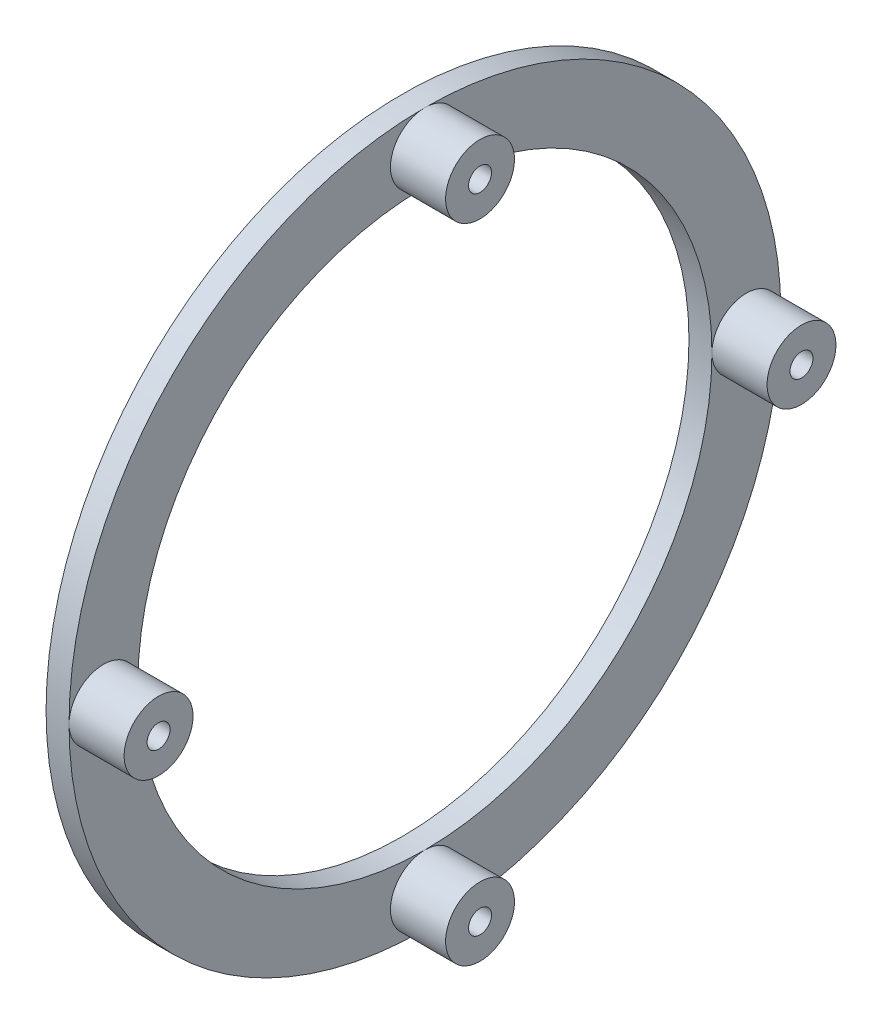
SolidWorks part; units mm, degrees
material "6061-T6 (SS)"
ref_plane "Front Plane" through (0, 0, 0) normal (0, 0, 1) x (1, 0, 0)
ref_plane "Top Plane" through (0, 0, 0) normal (0, 1, 0) x (1, 0, 0)
ref_plane "Right Plane" through (0, 0, 0) normal (1, 0, 0) x (0, 0, -1)
sketch "Sketch1" plane through (0, 0, 0) normal (1, 0, 0) x (0, 0, -1)
  circle A0 centre (0, 0) radius 98.425
  circle A1 centre (0, 0) radius 79.375
  dimension "D1" = 196.85
  dimension "D2" = 158.75
extrude "Boss-Extrude1" add sketch "Sketch1" along normal blind 6.35
sketch "Sketch2" plane through (0, 0, 0) normal (1, 0, 0) x (0, 0, -1)
  circle A0 centre (0, 0) radius 88.9 construction
  circle A1 centre (88.9, 0) radius 9.525
  dimension "D1" = 177.8
  dimension "D2" = 19.05
extrude "Boss-Extrude2" add sketch "Sketch2" along normal blind 15.24 from surface at 6.35 starting at face at (6.35, 0, -98.425)
hole_wizard "1/4 (0.2500) Dowel Hole1" positions "Sketch3" profile "Sketch4" hole size "1/4" standard "ANSI Inch"
sketch "Sketch3" plane through (21.59, 0, 0) normal (1, 0, 0) x (0, 0, -1)
  point P0 (88.9, 0)
sketch "Sketch4" plane through (21.59, 0, -88.9) normal (0, 1, 0) x (0, 0, -1)
  line L0 (0, 0) -> (0, 14.6077)
  line L1 (0, 14.6077) -> (3.175, 12.7)
  line L2 (3.175, 12.7) -> (3.175, 0)
  line L5 (3.175, 0) -> (0, 0)
  line L10 (0, 14.6077) -> (-3.175, 12.7) construction
  line L11 (0, -6.35) -> (0, 107.95) construction
  dimension "Hole Dia." = 6.35
  dimension "Hole Depth" = 12.7
  dimension "Drill Angle" = 118
pattern_circular "CirPattern2" count 4 over 360 about axis through (0, 0, 0) along (1, 0, 0) of "Boss-Extrude2", "1/4 (0.2500) Dowel Hole1"
